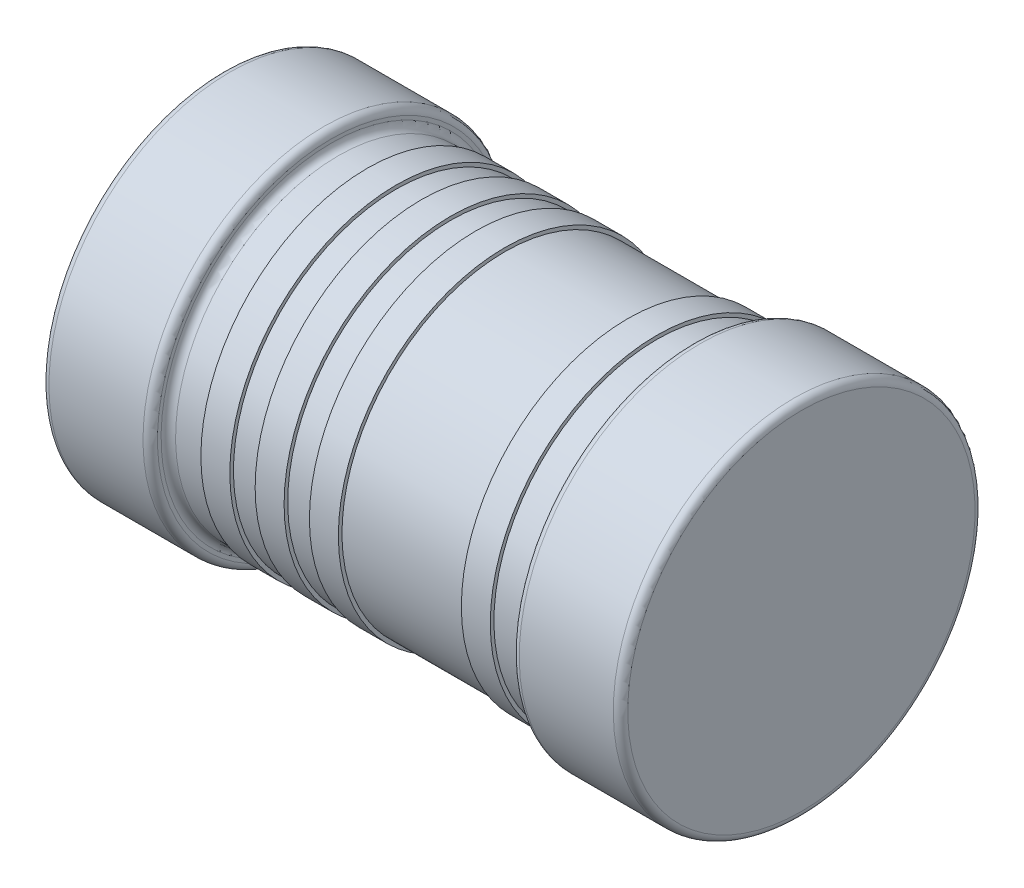
SolidWorks part; units mm, degrees
ref_plane "Front Plane" through (0, 0, 0) normal (0, 0, 1) x (1, 0, 0)
ref_plane "Top Plane" through (0, 0, 0) normal (0, 1, 0) x (1, 0, 0)
ref_plane "Right Plane" through (0, 0, 0) normal (1, 0, 0) x (0, 0, -1)
sketch "Sketch1" plane through (0, 0, 0) normal (0, 0, 1) x (1, 0, 0)
  line L0 (-0.8, 0.5) -> (0.8, 0.5)
  line L1 (0, 0) -> (0, 0.5) construction
  line L2 (-0.8, 0.5) -> (-3.0256, 0.5) construction
  line L3 (0.8, 0.5) -> (0.8, 0.02)
  line L4 (-0.78, 0) -> (-0.52, 0)
  line L5 (-0.8, 0.02) -> (-0.8, 0.5)
  line L6 (-0.5, 0.02) -> (-0.5, 0.03)
  line L7 (-0.48, 0.05) -> (-0.4, 0.05)
  line L8 (0.5, 0.03) -> (0.5, 0.02)
  line L9 (0.52, 0) -> (0.78, 0)
  line L10 (-0.4, 0.05) -> (-0.4, 0.04)
  line L11 (-0.4, 0.04) -> (-0.32, 0.04)
  line L12 (-0.32, 0.04) -> (-0.32, 0.05)
  line L13 (-0.25, 0.05) -> (-0.25, 0.04)
  line L14 (-0.25, 0.04) -> (-0.17, 0.04)
  line L15 (-0.17, 0.04) -> (-0.17, 0.05)
  line L16 (-0.02, 0.04) -> (-0.1, 0.04)
  line L17 (-0.1, 0.04) -> (-0.1, 0.05)
  line L18 (0.4, 0.05) -> (0.48, 0.05)
  line L19 (-0.02, 0.04) -> (-0.02, 0.05)
  line L20 (0.4, 0.05) -> (0.4, 0.04)
  line L21 (0.4, 0.04) -> (0.32, 0.04)
  line L22 (0.32, 0.04) -> (0.32, 0.05)
  line L23 (-0.36, 0.04) -> (-0.36, -0.0114) construction
  line L24 (-0.21, 0.04) -> (-0.21, -0.0114) construction
  line L25 (-0.06, 0.04) -> (-0.06, -0.0151) construction
  line L26 (0.36, 0.04) -> (0.36, -0.0151) construction
  line L27 (-0.02, 0.05) -> (0.32, 0.05)
  line L28 (-0.17, 0.05) -> (-0.1, 0.05)
  line L29 (-0.32, 0.05) -> (-0.25, 0.05)
  arc A0 (0.8, 0.02) -> (0.78, 0) centre (0.78, 0.02) cw
  arc A1 (0.52, 0) -> (0.5, 0.02) centre (0.52, 0.02) cw
  arc A2 (0.5, 0.03) -> (0.48, 0.05) centre (0.48, 0.03) ccw
  arc A3 (-0.48, 0.05) -> (-0.5, 0.03) centre (-0.48, 0.03) ccw
  arc A4 (-0.5, 0.02) -> (-0.52, 0) centre (-0.52, 0.02) cw
  arc A5 (-0.8, 0.02) -> (-0.78, 0) centre (-0.78, 0.02) ccw
  point P15 (0.8, 0)
  point P18 (0.5, 0)
  dimension "D5" = 0.02
  dimension "D1" = 1.6
  dimension "D2" = 0.3
  dimension "D3" = 0.05
  dimension "D4" = 0.5
  dimension "D6" = 0.08
  dimension "D7" = 0.01
  dimension "D8" = 0.15
  dimension "D9" = 0.15
  dimension "D10" = 0.06
  dimension "D11" = 0.36
revolve "Revolve1" add sketch "Sketch1" angle 360 about L2
